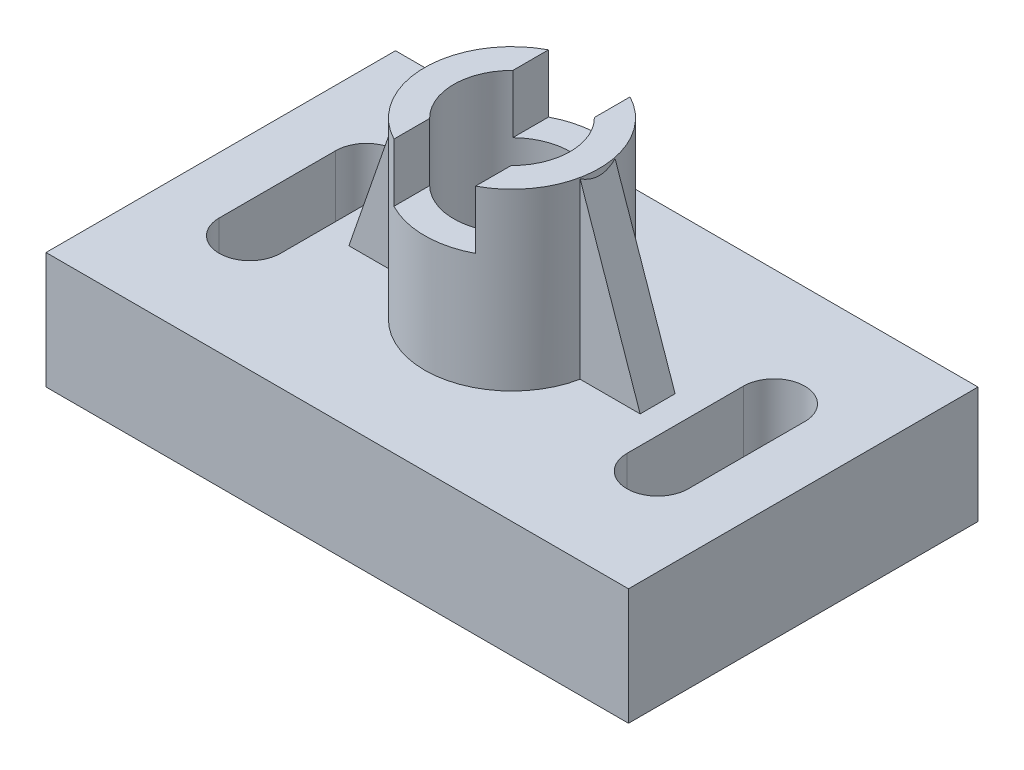
SolidWorks part; units mm, degrees
ref_plane "Front Plane" through (0, 0, 0) normal (0, 0, 1) x (1, 0, 0)
ref_plane "Top Plane" through (0, 0, 0) normal (0, 1, 0) x (1, 0, 0)
ref_plane "Right Plane" through (0, 0, 0) normal (1, 0, 0) x (0, 0, -1)
sketch "Sketch1" plane through (0, 0, 0) normal (0, 1, 0) x (1, 0, 0)
  line L0 (-35, 10) -> (-35, -10) construction
  line L1 (-50, 30) -> (50, 30)
  line L2 (-50, 30) -> (-50, -30)
  line L3 (-50, -30) -> (50, -30)
  line L4 (50, 30) -> (50, -30)
  line L5 (-50, 30) -> (50, -30) construction
  line L6 (-50, -30) -> (50, 30) construction
  line L7 (-29.7317, 10) -> (-29.7317, -10)
  line L8 (-40.2683, 10) -> (-40.2683, -10)
  line L9 (-35, 10) -> (-35, -10) construction
  line L10 (-25.0488, 10) -> (-25.0488, -10)
  line L11 (-44.9512, 10) -> (-44.9512, -10)
  line L12 (0, 30) -> (0, -30) construction
  line L15 (35, 10) -> (35, -10) construction
  line L18 (29.7317, 10) -> (29.7317, -10)
  line L19 (40.2683, 10) -> (40.2683, -10)
  line L20 (35, 10) -> (35, -10) construction
  line L21 (25.0488, 10) -> (25.0488, -10)
  line L22 (44.9512, 10) -> (44.9512, -10)
  arc A0 (-29.7317, 10) -> (-40.2683, 10) centre (-35, 10) ccw
  arc A1 (-40.2683, -10) -> (-29.7317, -10) centre (-35, -10) ccw
  arc A2 (-25.0488, 10) -> (-44.9512, 10) centre (-35, 10) ccw
  arc A3 (-44.9512, -10) -> (-25.0488, -10) centre (-35, -10) ccw
  arc A8 (29.7317, 10) -> (40.2683, 10) centre (35, 10) cw
  arc A9 (40.2683, -10) -> (29.7317, -10) centre (35, -10) cw
  arc A10 (25.0488, 10) -> (44.9512, 10) centre (35, 10) cw
  arc A11 (44.9512, -10) -> (25.0488, -10) centre (35, -10) cw
  point P0 (0, 0)
  point P8 (-35, 0)
  point P13 (-35, 0)
  point P24 (35, 0)
  point P31 (35, 0)
  dimension "D1" = 60
  dimension "D2" = 100
  dimension "D3" = 20
  dimension "D4" = 20
  dimension "D5" = 15
extrude "Boss-Extrude2" add sketch "Sketch1" along normal blind 20 contours L4 L1 L2 L3 A3 L11 A2 L10 L22 A11 L21 A10 | L11 A3 L10 A2 A1 L8 A0 L7 | A11 L22 A10 L21 L19 A9 L18 A8
sketch "Sketch2" plane through (0, 20, 0) normal (0, 1, 0) x (1, 0, 0)
  circle A0 centre (0, 0) radius 15
  circle A1 centre (0, 0) radius 10
  circle A2 centre (0, 0) radius 5
  dimension "D1" = 30
  dimension "D2" = 20
  dimension "D3" = 10
extrude "Boss-Extrude3" add sketch "Sketch2" along normal blind 30 contours A0 A1
sketch "Sketch3" plane through (0, 50, 0) normal (0, 1, 0) x (1, 0, 0)
  line L1 (7, -17.601) -> (-7, -17.601)
  line L2 (7, -17.601) -> (7, 17.601)
  line L3 (7, 17.601) -> (-7, 17.601)
  line L4 (-7, -17.601) -> (-7, 17.601)
  line L5 (7, -17.601) -> (-7, 17.601) construction
  line L6 (7, 17.601) -> (-7, -17.601) construction
  point P0 (0, 0)
  dimension "D1" = 14
extrude "Cut-Extrude1" cut sketch "Sketch3" against normal blind 10 contours L2 L1 L4 L3
sketch "Sketch19" plane through (0, 0, 0) normal (0, 0, 1) x (1, 0, 0)
  line L0 (15, 48.9276) -> (25, 20)
  line L1 (15, 20) -> (15, 50) construction
  line L2 (-50, 20) -> (50, 20) construction
  dimension "D1" = 10
rib "Rib4" sketch "Sketch19" sketch "Sketch19" thickness 6 extrusion direction parallel to sketch draft on no parameters "D1"=6
mirror "Mirror2" about plane through (0, 0, 0) normal (1, 0, 0) of "Rib4"
